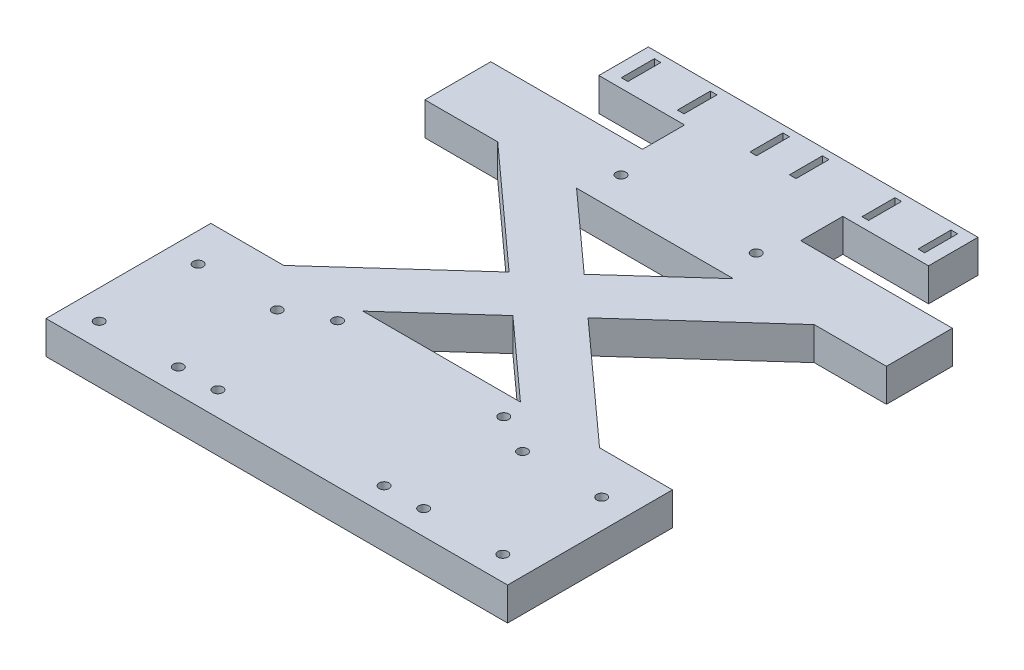
SolidWorks part; units mm, degrees
ref_plane "前视基准面" through (0, 0, 0) normal (0, 0, 1) x (1, 0, 0)
ref_plane "上视基准面" through (0, 0, 0) normal (0, 1, 0) x (1, 0, 0)
ref_plane "右视基准面" through (0, 0, 0) normal (1, 0, 0) x (0, 0, -1)
sketch "草图1" plane through (0, 0, 0) normal (0, 1, 0) x (1, 0, 0)
  line L0 (-61.2072, 12.3467) -> (-61.2072, 10.8467) construction
  line L1 (-68, 25) -> (-47.9, 25)
  line L2 (-70, 23) -> (-70, -23)
  line L3 (-68, -25) -> (68, -25)
  line L4 (70, 23) -> (70, -23)
  line L5 (-68, 109.9109) -> (-70, 109.9109)
  line L6 (-70, 109.9109) -> (-70, 107.9109)
  line L7 (-61.2072, 12.3467) -> (-59.7072, 12.3467) construction
  line L8 (-70, 91.9109) -> (-70, 89.9109)
  line L9 (-61.2072, -17.6533) -> (-59.7072, -17.6533) construction
  line L12 (68, 89.9109) -> (48.1, 89.9109)
  line L13 (-70, 91.9109) -> (-70, 107.9109)
  line L17 (68, 109.9109) -> (24, 109.9109)
  line L18 (70, 91.9109) -> (70, 107.9109)
  line L19 (-70, 89.9109) -> (-68, 89.9109)
  line L23 (-47.9, 89.9109) -> (-68, 89.9109)
  line L31 (-24, 109.9109) -> (-68, 109.9109)
  line L32 (68, 89.9109) -> (70, 89.9109)
  line L33 (-24, 109.9109) -> (-24, 114.8552)
  line L34 (24, 109.9109) -> (24, 114.8552)
  line L38 (-24, 114.8552) -> (-24, 122.6841)
  line L39 (-50, 137.6841) -> (50, 137.6841)
  line L41 (-50, 122.6841) -> (-24, 122.6841)
  line L43 (70, 89.9109) -> (70, 91.9109)
  line L45 (24, 114.8552) -> (24, 122.6841)
  line L47 (5, 125.502) -> (7, 125.502)
  line L48 (5, 125.502) -> (5, 135.502)
  line L49 (5, 135.502) -> (7, 135.502)
  line L50 (7, 125.502) -> (7, 135.502)
  line L51 (70, 107.9109) -> (70, 109.9109)
  line L52 (70, 109.9109) -> (68, 109.9109)
  line L54 (-5, 125.502) -> (-7, 125.502)
  line L55 (-7, 125.502) -> (-7, 135.502)
  line L56 (-5, 125.502) -> (-5, 135.502)
  line L57 (-5, 135.502) -> (-7, 135.502)
  line L59 (24, 122.6841) -> (50, 122.6841)
  line L66 (29, 125.502) -> (27, 125.502)
  line L67 (27, 125.502) -> (27, 135.502)
  line L68 (29, 125.502) -> (29, 135.502)
  line L69 (29, 135.502) -> (27, 135.502)
  line L70 (46, 125.502) -> (44, 125.502)
  line L71 (44, 125.502) -> (44, 135.502)
  line L72 (46, 125.502) -> (46, 135.502)
  line L73 (46, 135.502) -> (44, 135.502)
  line L74 (-46, 125.502) -> (-44, 125.502)
  line L75 (-46, 125.502) -> (-46, 135.502)
  line L76 (-44, 125.502) -> (-44, 135.502)
  line L77 (-46, 135.502) -> (-44, 135.502)
  line L78 (-29, 135.502) -> (-27, 135.502)
  line L79 (-29, 125.502) -> (-27, 125.502)
  line L80 (-29, 125.502) -> (-29, 135.502)
  line L81 (-27, 125.502) -> (-27, 135.502)
  line L82 (-50, 137.6841) -> (-50, 122.6841)
  line L83 (50, 137.6841) -> (50, 122.6841)
  line L87 (-47.9, 89.9109) -> (-11.9724, 57.4305)
  line L92 (47.9, 25) -> (12.0224, 57.3854)
  line L95 (-23.7897, 89.7117) -> (23.7897, 89.7117)
  line L97 (23.7897, 89.7117) -> (0, 68.2376)
  line L98 (-23.9, 25) -> (0.0332, 46.5768)
  line L101 (-23.9, 25) -> (23.9, 25)
  line L102 (47.9, 25) -> (68, 25)
  line L117 (-70, 23) -> (-70, 25)
  line L118 (-68, 25) -> (-70, 25)
  line L119 (-70, -23) -> (-70, -25)
  line L120 (-70, -25) -> (-68, -25)
  line L121 (68, -25) -> (70, -25)
  line L122 (70, -25) -> (70, -23)
  line L123 (70, 23) -> (70, 25)
  line L124 (70, 25) -> (68, 25)
  line L125 (0.0332, 46.5768) -> (23.9, 25)
  line L126 (12.0224, 57.3854) -> (48.1, 89.9109)
  line L127 (-11.9724, 57.4305) -> (-47.9, 25)
  line L128 (0, 68.2376) -> (-23.7897, 89.7117)
  line L129 (-61.2072, -16.1533) -> (-61.2072, -17.6533) construction
  line L130 (-38.7072, 12.3467) -> (-37.2072, 12.3467) construction
  line L131 (-38.7072, -17.6533) -> (-37.2072, -17.6533) construction
  circle A0 centre (-61.2072, 12.3467) radius 1.5
  circle A1 centre (-37.2072, 12.3467) radius 1.5
  circle A2 centre (-37.2072, -17.6533) radius 1.5
  circle A3 centre (-61.2072, -17.6533) radius 1.5
  circle A4 centre (61.2072, -17.6533) radius 1.5
  circle A5 centre (37.2072, -17.6533) radius 1.5
  circle A6 centre (37.2072, 12.3467) radius 1.5
  circle A7 centre (61.2072, 12.3467) radius 1.5
  circle A10 centre (-20.5, 99.9109) radius 1.5
  circle A11 centre (20.5, 99.9109) radius 1.5
  circle A25 centre (-25.2101, 18.6285) radius 1.5
  circle A26 centre (25.2101, 18.6285) radius 1.5
  circle A27 centre (-25.2101, -17.6533) radius 1.5
  circle A28 centre (25.2101, -17.6533) radius 1.5
  point P0 (0, 0)
  point P35 (1.8118, 98.7827)
  point P40 (6, 130.502)
  point P56 (6, 130.502)
  point P141 (-50, 130.1841)
  dimension "D6" = 4
  dimension "D13" = 3
  dimension "D2" = 100
  dimension "D4" = 26
extrude "凸台-拉伸1" add sketch "草图1" along normal blind 10
